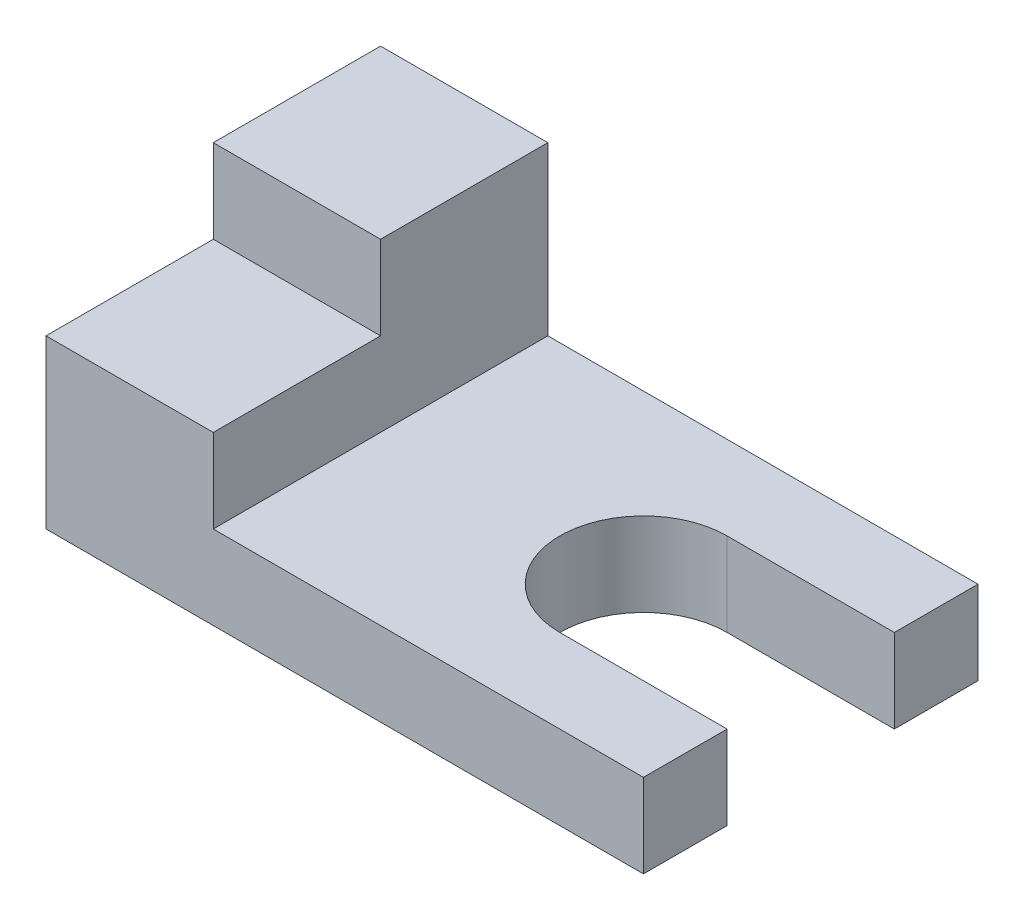
SolidWorks part; units mm, degrees
material "회주철"
ref_plane "정면" through (0, 0, 0) normal (0, 0, 1) x (1, 0, 0)
ref_plane "윗면" through (0, 0, 0) normal (0, 1, 0) x (1, 0, 0)
ref_plane "우측면" through (0, 0, 0) normal (1, 0, 0) x (0, 0, -1)
sketch "스케치1" plane through (0, 0, 0) normal (0, 0, 1) x (1, 0, 0)
  line L0 (14, 7) -> (14, 21)
  line L1 (0, 0) -> (50, 0)
  line L2 (0, 0) -> (0, 21)
  line L3 (0, 21) -> (14, 21)
  line L4 (50, 0) -> (50, 7)
  line L5 (14, 7) -> (50, 7)
  line L6 (14, 0) -> (14, 21) construction
  line L7 (0, 7) -> (50, 7) construction
  dimension "D1" = 21
  dimension "D2" = 14
  dimension "D3" = 7
  dimension "D4" = 50
extrude "보스-돌출1" add sketch "스케치1" along normal blind 28
sketch "스케치2" plane through (0, 21, 0) normal (0, 1, 0) x (1, 0, 0)
  line L3 (14, -14) -> (0, -14)
  line L11 (0, -14) -> (0, -28)
  line L12 (0, -28) -> (14, -28)
  line L13 (14, -28) -> (14, -14)
  dimension "D2" = 14
  dimension "D3" = 14
  dimension "D1" = 14
  dimension "D4" = 14
extrude "컷-돌출1" cut sketch "스케치2" against normal blind 7
sketch "스케치3" plane through (0, 0, 0) normal (0, 1, 0) x (1, 0, 0)
  line L1 (50, -28) -> (50, 0) construction
  line L2 (36, -7) -> (50, -7)
  line L3 (50, -7) -> (50, -21)
  line L4 (50, -21) -> (36, -21)
  arc A0 (36, -7) -> (36, -21) centre (36, -14) ccw
  dimension "D1" = 36
  dimension "D3" = 14
  dimension "D2" = 7
extrude "컷-돌출2" cut sketch "스케치3" along normal up to next
